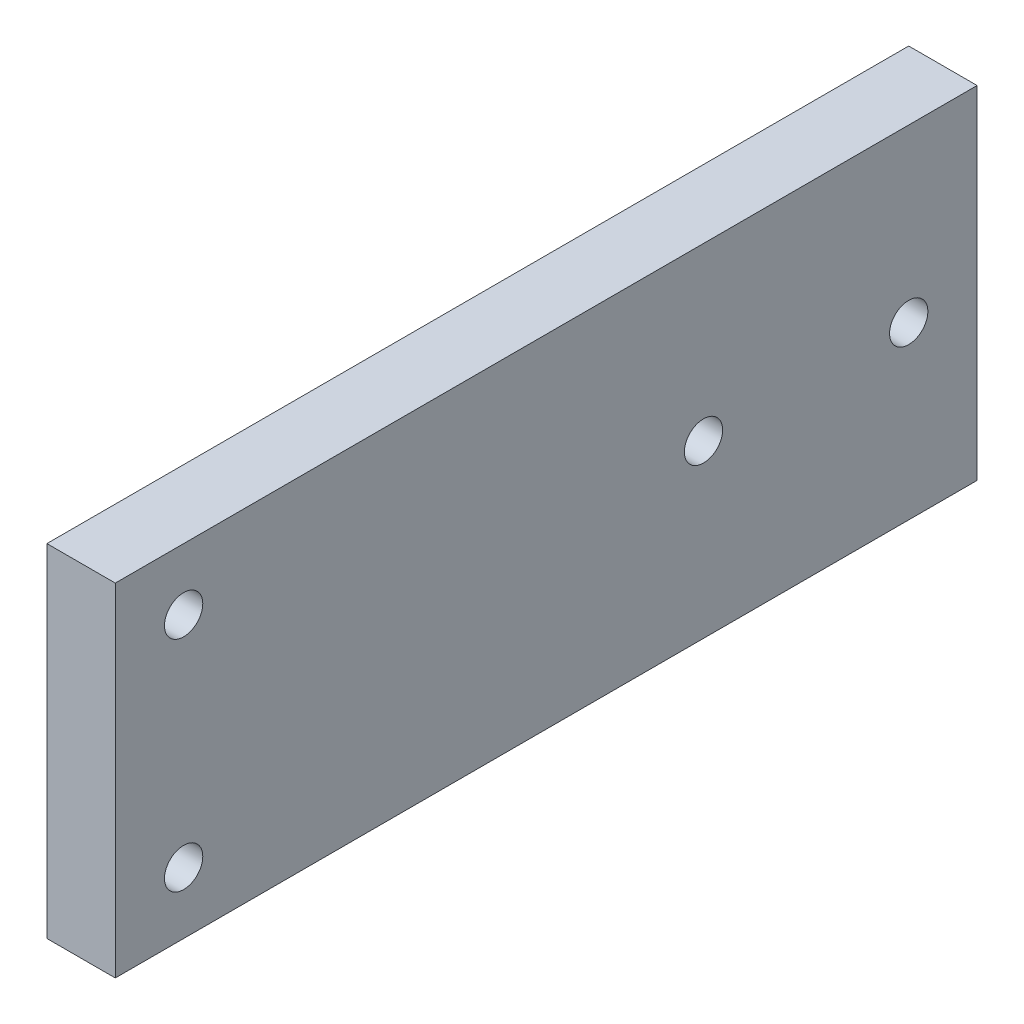
SolidWorks part; units mm, degrees
ref_plane "前视基准面" through (0, 0, 0) normal (0, 0, 1) x (1, 0, 0)
ref_plane "上视基准面" through (0, 0, 0) normal (0, 1, 0) x (1, 0, 0)
ref_plane "右视基准面" through (0, 0, 0) normal (1, 0, 0) x (0, 0, -1)
sketch "草图1" plane through (0, 0, 0) normal (1, 0, 0) x (0, 0, -1)
  line L0 (62.995, 0) -> (0, 0)
  line L1 (0, 25) -> (62.995, 25)
  line L2 (62.995, 0) -> (62.995, 25)
  line L3 (0, 25) -> (0, 0)
  circle A0 centre (4.995, 4.5) radius 1.4
  circle A1 centre (4.995, 20.5) radius 1.4
  circle A2 centre (42.995, 12.5) radius 1.4
  circle A3 centre (57.995, 12.5) radius 1.4
extrude "凸台-拉伸1" add sketch "草图1" along normal mid plane 5
